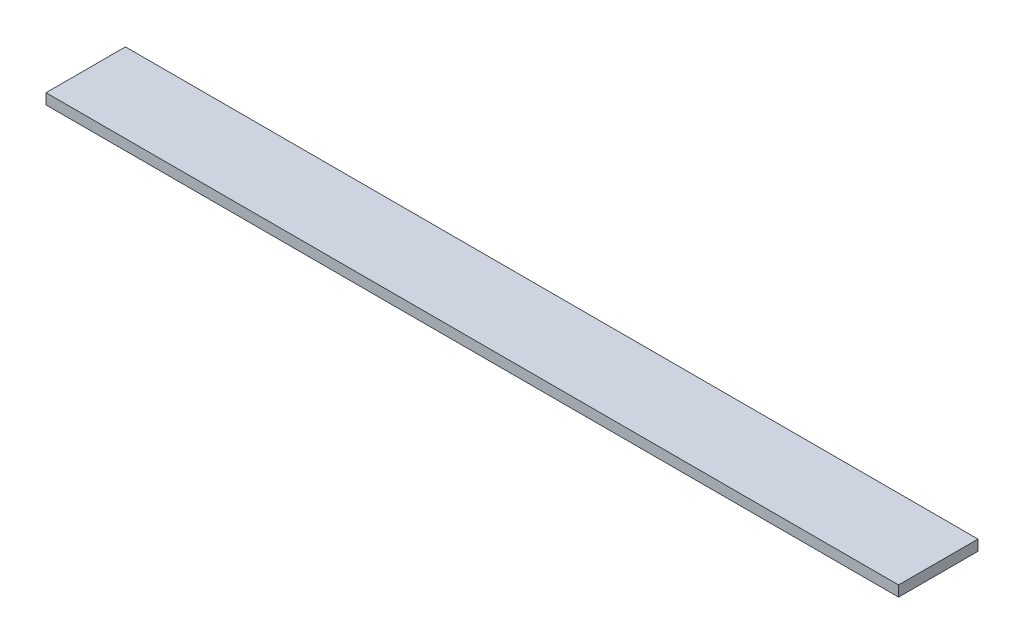
SolidWorks part; units mm, degrees
ref_plane "Спереди" through (0, 0, 0) normal (0, 0, 1) x (1, 0, 0)
ref_plane "Сверху" through (0, 0, 0) normal (0, 1, 0) x (1, 0, 0)
ref_plane "Справа" through (0, 0, 0) normal (1, 0, 0) x (0, 0, -1)
sketch "Эскиз1" plane through (0, 0, 0) normal (1, 0, 0) x (0, 0, -1)
  line L1 (-15, -2) -> (15, -2)
  line L2 (-15, -2) -> (-15, 2)
  line L3 (-15, 2) -> (15, 2)
  line L4 (15, -2) -> (15, 2)
  line L5 (-15, -2) -> (15, 2) construction
  line L6 (-15, 2) -> (15, -2) construction
  point P0 (0, 0)
  dimension "D1" = 4
  dimension "D2" = 30
extrude "Бобышка-Вытянуть1" add sketch "Эскиз1" along normal blind 322
